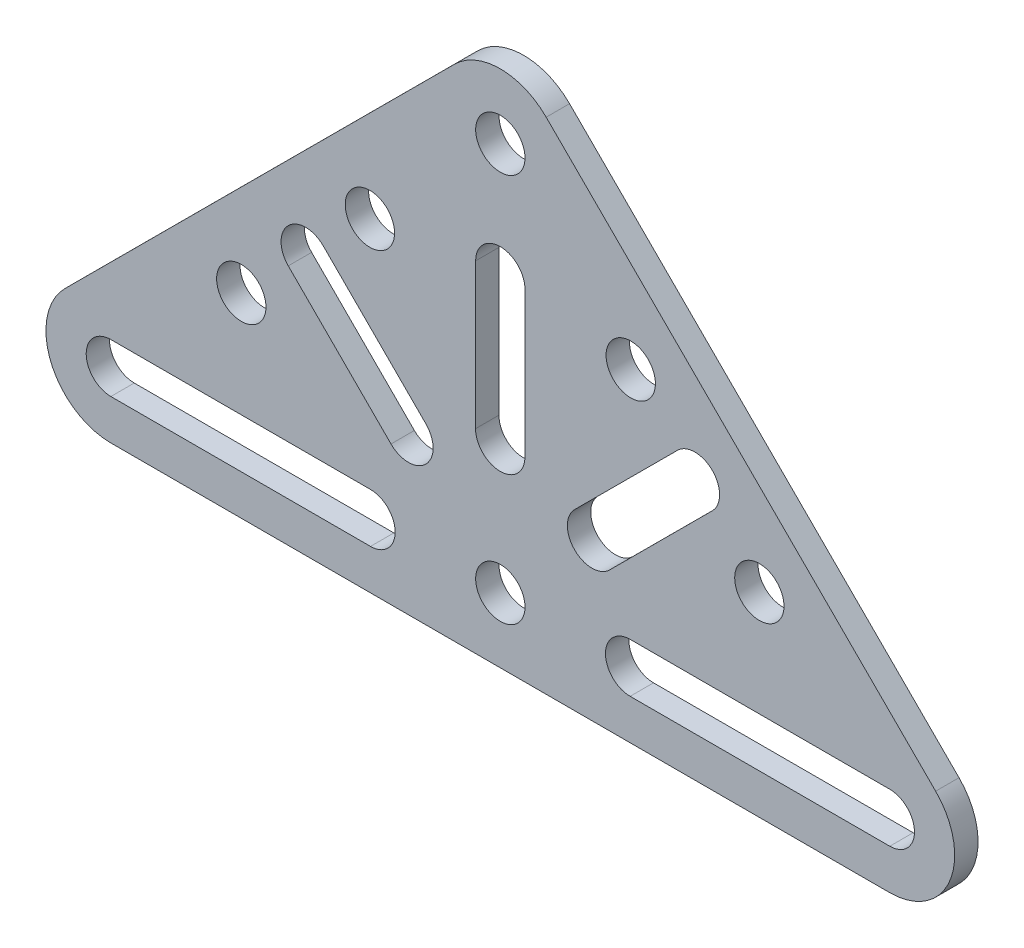
SolidWorks part; units mm, degrees
ref_plane "Front Plane" through (0, 0, 0) normal (0, 0, 1) x (1, 0, 0)
ref_plane "Top Plane" through (0, 0, 0) normal (0, 1, 0) x (1, 0, 0)
ref_plane "Right Plane" through (0, 0, 0) normal (1, 0, 0) x (0, 0, -1)
sketch "Sketch1" plane through (0, 0, 0) normal (0, 0, 1) x (1, 0, 0)
  line L0 (0, 0) -> (0, 38.0526) construction
  line L1 (38.1, 0) -> (-38.1, 0) construction
  line L2 (-38.1, 0) -> (0, 38.0526) construction
  line L3 (38.1, 0) -> (0, 38.0526) construction
  line L4 (0, 0) -> (19.0381, 19.0381) construction
  line L5 (0, 0) -> (-19.0381, 19.0381) construction
  line L6 (-42.5873, 4.4929) -> (-4.4873, 42.5455)
  line L7 (42.5873, 4.4929) -> (4.4873, 42.5455)
  line L8 (38.1, -6.35) -> (-38.1, -6.35)
  line L9 (-53.4438, -6.35) -> (0, 47.0272) construction
  line L10 (53.4438, -6.35) -> (-53.4438, -6.35) construction
  line L11 (53.4438, -6.35) -> (0, 47.0272) construction
  arc A0 (-42.5873, 4.4929) -> (-38.1, -6.35) centre (-38.1, 0) ccw
  arc A1 (-4.4873, 42.5455) -> (4.4873, 42.5455) centre (0, 38.0526) cw
  arc A2 (42.5873, 4.4929) -> (38.1, -6.35) centre (38.1, 0) cw
  dimension "D5" = 6.35
  dimension "D1" = 45
  dimension "D2" = 76.2
  dimension "D3" = 53.848
  dimension "D4" = 6.35
extrude "Boss-Extrude1" add sketch "Sketch1" along normal blind 2.286
sketch "Sketch2" plane through (0, 0, 2.286) normal (0, 0, 1) x (1, 0, 0)
  line L0 (0, 0) -> (0, 38.0526) construction
  line L1 (-38.1, 0) -> (0, 38.0526) construction
  circle A0 centre (0, 0) radius 2.413
  circle A1 centre (0, 38.0526) radius 2.413
  circle A2 centre (-25.3401, 12.744) radius 2.413
  circle A3 centre (25.3401, 12.744) radius 2.413
  circle A4 centre (-12.7599, 25.3085) radius 2.413
  circle A5 centre (12.7599, 25.3085) radius 2.413
  dimension "D1" = 4.826
  dimension "D2" = 18.034
  dimension "D3" = 35.814
extrude "Cut-Extrude1" cut sketch "Sketch2" against normal through all
sketch "Sketch3" plane through (0, 0, 2.286) normal (0, 0, 1) x (1, 0, 0)
  line L1 (-38.1, 2.413) -> (-12.7, 2.413)
  line L3 (-38.1, -2.413) -> (-12.7, -2.413)
  arc A0 (-38.1, 2.413) -> (-38.1, -2.413) centre (-38.1, 0) ccw
  arc A1 (-12.7, 2.413) -> (-12.7, -2.413) centre (-12.7, 0) cw
  circle A2 centre (0, 0) radius 2.413 construction
  dimension "D1" = 25.4
extrude "Cut-Extrude2" cut sketch "Sketch3" against normal through all
mirror "Mirror1" about plane through (0, 0, 0) normal (1, 0, 0) of "Cut-Extrude2"
sketch "Sketch4" plane through (0, 0, 2.286) normal (0, 0, 1) x (1, 0, 0)
  line L0 (-20.7454, 17.3329) -> (-10.6938, 7.2688)
  line L2 (0, 0) -> (-19.0381, 19.0381) construction
  line L3 (-17.3308, 20.7433) -> (-7.2792, 10.6792)
  line L4 (-38.1, 0) -> (0, 38.0526) construction
  arc A0 (-17.3308, 20.7433) -> (-20.7454, 17.3329) centre (-19.0381, 19.0381) ccw
  arc A1 (-7.2792, 10.6792) -> (-10.6938, 7.2688) centre (-8.9865, 8.974) cw
  circle A2 centre (-25.3401, 12.744) radius 2.413 construction
  dimension "D1" = 14.224
extrude "Cut-Extrude3" cut sketch "Sketch4" against normal through all
pattern_circular "CirPattern1" count 3 over 90 about axis through (0, 0, 0) along (0, 0, 1) of "Cut-Extrude3"
